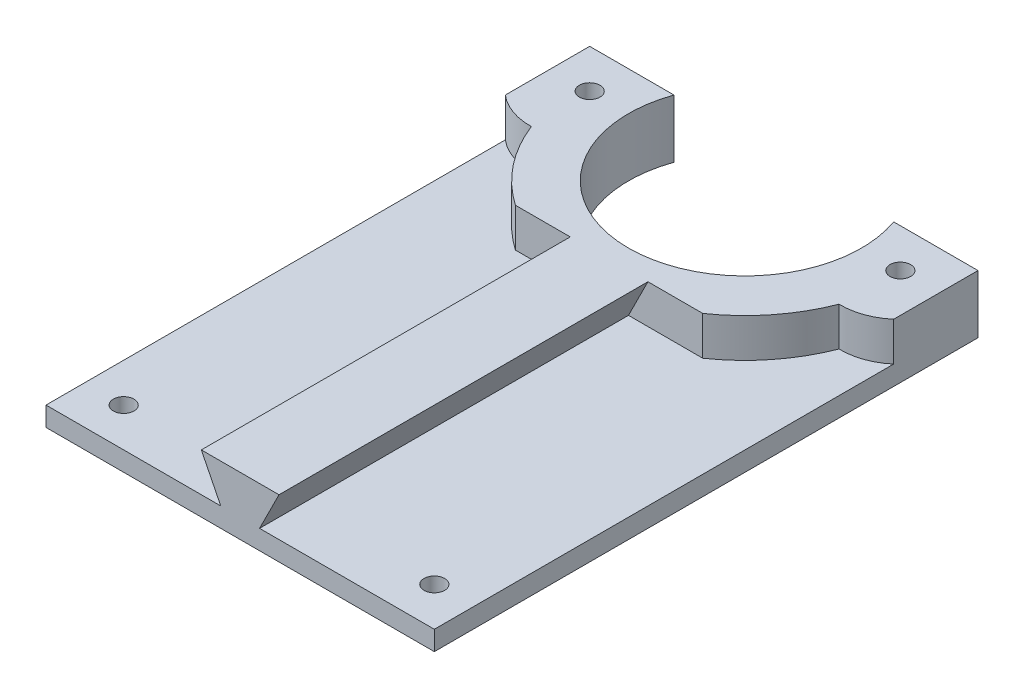
SolidWorks part; units mm, degrees
ref_plane "Front Plane" through (0, 0, 0) normal (0, 0, 1) x (1, 0, 0)
ref_plane "Top Plane" through (0, 0, 0) normal (0, 1, 0) x (1, 0, 0)
ref_plane "Right Plane" through (0, 0, 0) normal (1, 0, 0) x (0, 0, -1)
sketch "Sketch1" plane through (0, 0, 0) normal (0, 1, 0) x (1, 0, 0)
  line L1 (63.5, -88.9) -> (-63.5, -88.9)
  line L2 (63.5, -88.9) -> (63.5, 88.9)
  line L3 (63.5, 88.9) -> (-63.5, 88.9)
  line L4 (-63.5, -88.9) -> (-63.5, 88.9)
  line L5 (63.5, -88.9) -> (-63.5, 88.9) construction
  line L6 (63.5, 88.9) -> (-63.5, -88.9) construction
  point P0 (0, 0)
  dimension "D1" = 127
  dimension "D2" = 177.8
extrude "Boss-Extrude1" add sketch "Sketch1" along normal blind 6.35
hole_wizard "H (0.266) Diameter Hole1" positions "Sketch2" profile "Sketch3" hole size "H" standard "ANSI Inch"
sketch "Sketch2" plane through (0, 6.35, 0) normal (0, 1, 0) x (1, 0, 0)
  line L1 (50.8, -76.2) -> (-50.8, -76.2)
  line L2 (50.8, -76.2) -> (50.8, 76.2)
  line L3 (50.8, 76.2) -> (-50.8, 76.2)
  line L4 (-50.8, -76.2) -> (-50.8, 76.2)
  line L5 (50.8, -76.2) -> (-50.8, 76.2) construction
  line L6 (50.8, 76.2) -> (-50.8, -76.2) construction
  line L7 (63.5, 88.9) -> (-63.5, 88.9) construction
  line L8 (-63.5, -88.9) -> (63.5, -88.9) construction
  point P2 (-50.8, 76.2)
  point P95 (50.8, -76.2)
  point P96 (50.8, 76.2)
  point P97 (-50.8, -76.2)
  dimension "D1" = 101.6
  dimension "D2" = 12.7
  dimension "D3" = 12.7
sketch "Sketch3" plane through (-50.8, 6.35, -76.2) normal (1, 0, 0) x (0, 0, 1)
  line L0 (0, 0) -> (0, 18.5398)
  line L1 (0, 18.5398) -> (3.3782, 16.51)
  line L2 (3.3782, 16.51) -> (3.3782, 0)
  line L5 (3.3782, 0) -> (0, 0)
  line L10 (0, 18.5398) -> (-3.3782, 16.51) construction
  line L11 (0, -6.35) -> (0, 107.95) construction
  dimension "Hole Dia." = 6.7564
  dimension "Hole Depth" = 16.51
  dimension "Drill Angle" = 118
sketch "Sketch4" plane through (0, 6.35, 0) normal (0, 1, 0) x (1, 0, 0)
  line L0 (0, 0) -> (0, 76.2) construction
  line L1 (63.5, 88.9) -> (-63.5, 88.9) construction
  circle A0 centre (0, 76.2) radius 38.1
  dimension "D1" = 76.2
  dimension "D2" = 12.7
extrude "Cut-Extrude1" cut sketch "Sketch4" against normal blind 6.35
sketch "Sketch5" plane through (0, 6.35, 0) normal (0, 1, 0) x (1, 0, 0)
  line L5 (-35.921, 88.9) -> (-63.5, 88.9)
  line L6 (-63.5, 88.9) -> (-63.5, -88.9)
  line L7 (-63.5, -88.9) -> (63.5, -88.9)
  line L8 (63.5, -88.9) -> (63.5, 88.9)
  line L9 (63.5, 88.9) -> (35.921, 88.9)
  line L10 (-35.921, 88.9) -> (-63.5, 88.9)
  line L11 (-63.5, 88.9) -> (-63.5, -88.9)
  line L12 (-63.5, -88.9) -> (63.5, -88.9)
  line L13 (63.5, -88.9) -> (63.5, 88.9)
  line L14 (63.5, 88.9) -> (35.921, 88.9)
  circle A0 centre (0, 76.2) radius 53.975
  circle A1 centre (50.8, 76.2) radius 3.3782
  circle A2 centre (50.8, 76.2) radius 3.3782
  circle A3 centre (-50.8, 76.2) radius 3.3782
  circle A4 centre (-50.8, 76.2) radius 3.3782
  arc A5 (-35.921, 88.9) -> (35.921, 88.9) centre (0, 76.2) ccw
  arc A6 (-35.921, 88.9) -> (35.921, 88.9) centre (0, 76.2) ccw
  circle A9 centre (-50.8, 76.2) radius 19.5621
  circle A10 centre (50.8, 76.2) radius 19.5621
  arc M9 (35.921, 88.9) -> (-35.921, 88.9) centre (0, 76.2) cw
  line M10 (-35.921, 88.9) -> (-63.5, 88.9)
  line M11 (-63.5, 88.9) -> (-63.5, -88.9)
  line M14 (63.5, 88.9) -> (35.921, 88.9)
  circle M15 centre (-50.8, 76.2) radius 3.3782
  circle M17 centre (50.8, 76.2) radius 3.3782
  dimension "D4" = 15.875
  dimension "D1" = 0
  dimension "D2" = 0
  dimension "D3" = 0
extrude "Boss-Extrude2" add sketch "Sketch5" along normal blind 12.7 contours A9 A0 L10 M11 M15 | A0 A9 A6 M10 M15 | A10 A6 A9 A0 | A10 A0 L14 M9 M17 | A0 A10 L13 M14 M17
ref_plane "Plane1" through (0, 0, 88.9) normal (0, 0, 1) x (1, 0, 0)
sketch "Sketch6" plane through (0, 0, 88.9) normal (0, 0, 1) x (1, 0, 0)
  line L0 (0, 6.35) -> (-6.35, 6.35) construction
  line L1 (-63.5, 6.35) -> (63.5, 6.35) construction
  line L2 (0, 6.35) -> (6.35, 6.35) construction
  line L3 (-6.35, 6.35) -> (-12.7, 19.05)
  line L4 (-12.7, 19.05) -> (12.7, 19.05)
  line L5 (12.7, 19.05) -> (6.35, 6.35)
  line L10 (-63.5, 0) -> (63.5, 0)
  line L11 (63.5, 0) -> (63.5, 6.35)
  line L12 (63.5, 6.35) -> (-63.5, 6.35)
  line L13 (-63.5, 6.35) -> (-63.5, 0)
  line L14 (-63.5, 0) -> (63.5, 0)
  line L15 (63.5, 0) -> (63.5, 6.35)
  line L16 (63.5, 6.35) -> (-63.5, 6.35)
  line L17 (-63.5, 6.35) -> (-63.5, 0)
  dimension "D1" = 6.35
  dimension "D2" = 12.7
  dimension "D3" = 6.35
  dimension "D4" = 6.35
  dimension "D5" = 0
extrude "Boss-Extrude3" add sketch "Sketch6" against normal blind 121.666 contours L16 L5 L4 L3
sketch "Sketch7" plane through (0, 0, 88.9) normal (0, 0, 1) x (1, 0, 0)
  line L0 (6.35, 6.35) -> (12.7, 19.05) construction
  line L1 (23.0151, -32.8134) -> (-23.0151, -32.8134)
  line L2 (23.0151, -32.8134) -> (23.0151, 32.8134)
  line L3 (23.0151, 32.8134) -> (-23.0151, 32.8134)
  line L4 (-23.0151, -32.8134) -> (-23.0151, 32.8134)
  line L5 (23.0151, -32.8134) -> (-23.0151, 32.8134) construction
  line L6 (23.0151, 32.8134) -> (-23.0151, -32.8134) construction
  line L7 (50.3077, 6.35) -> (6.35, 6.35) construction
  line L8 (-63.5, 0) -> (63.5, 0)
  line L9 (63.5, 0) -> (63.5, 6.35)
  line L10 (63.5, 6.35) -> (6.35, 6.35)
  line L11 (6.35, 6.35) -> (12.7, 19.05)
  line L12 (12.7, 19.05) -> (-12.7, 19.05)
  line L13 (-12.7, 19.05) -> (-6.35, 6.35)
  line L14 (-6.35, 6.35) -> (-63.5, 6.35)
  line L15 (-63.5, 6.35) -> (-63.5, 0)
  line L16 (-63.5, 0) -> (63.5, 0)
  line L17 (63.5, 0) -> (63.5, 6.35)
  line L18 (63.5, 6.35) -> (6.35, 6.35)
  line L19 (6.35, 6.35) -> (12.7, 19.05)
  line L20 (12.7, 19.05) -> (-12.7, 19.05)
  line L21 (-12.7, 19.05) -> (-6.35, 6.35)
  line L22 (-6.35, 6.35) -> (-63.5, 6.35)
  line L23 (-63.5, 6.35) -> (-63.5, 0)
  line L24 (50.3077, 6.35) -> (50.3077, 19.05) construction
  line L25 (50.3077, 19.05) -> (12.7, 19.05) construction
  line L26 (-12.7, 19.05) -> (-6.35, 6.35) construction
  line L27 (-12.7, 19.05) -> (-50.3077, 19.05) construction
  line L28 (-50.3077, 19.05) -> (-50.3077, 6.35) construction
  line L29 (-6.35, 6.35) -> (-50.3077, 6.35) construction
  line L30 (6.35, 6.35) -> (12.7, 19.05)
  line L31 (50.3077, 6.35) -> (6.35, 6.35)
  line L32 (50.3077, 6.35) -> (50.3077, 19.05)
  line L33 (50.3077, 19.05) -> (12.7, 19.05)
  line L34 (-12.7, 19.05) -> (-6.35, 6.35)
  line L35 (-12.7, 19.05) -> (-50.3077, 19.05)
  line L36 (-50.3077, 19.05) -> (-50.3077, 6.35)
  line L37 (-6.35, 6.35) -> (-50.3077, 6.35)
  point P2 (0, 0)
  line M15 (63.5, 6.35) -> (6.35, 6.35)
  line M16 (6.35, 6.35) -> (12.7, 19.05)
  line M18 (-12.7, 19.05) -> (-6.35, 6.35)
  line M19 (-6.35, 6.35) -> (-63.5, 6.35)
  dimension "D1" = 0
extrude "Cut-Extrude2" cut sketch "Sketch7" against normal blind 120.65 contours L35 L36 L4 M19 | L35 L4 M18 M19 | L2 L33 M16 M15 | L32 L33 L2 L18
